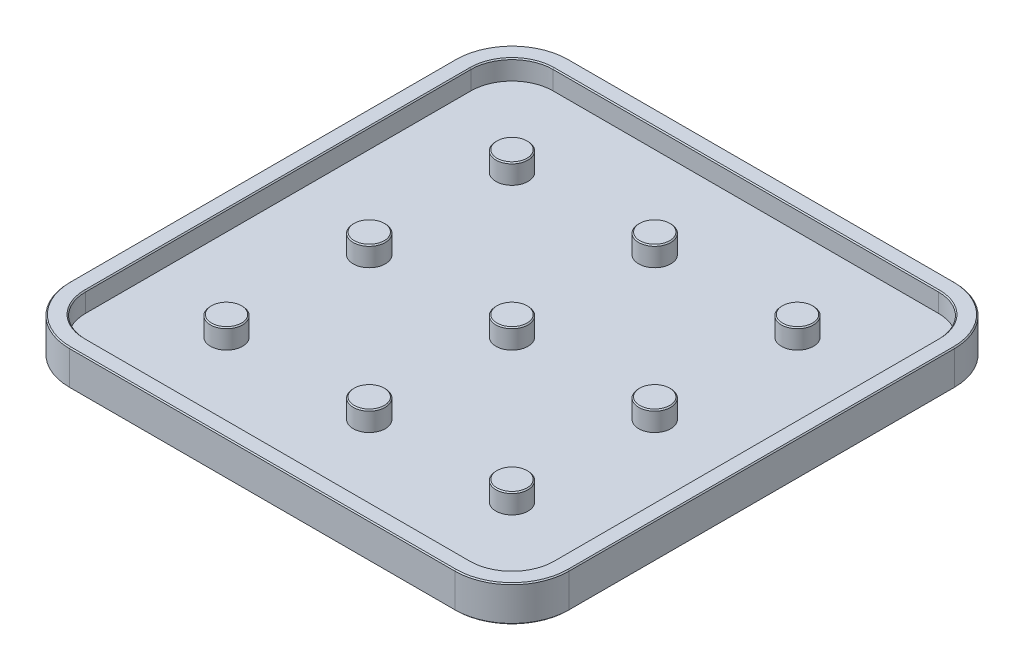
SolidWorks part; units mm, degrees
ref_plane "Front Plane" through (0, 0, 0) normal (0, 0, 1) x (1, 0, 0)
ref_plane "Top Plane" through (0, 0, 0) normal (0, 1, 0) x (1, 0, 0)
ref_plane "Right Plane" through (0, 0, 0) normal (1, 0, 0) x (0, 0, -1)
sketch "Sketch1" plane through (0, 0, 0) normal (0, 1, 0) x (1, 0, 0)
  line L1 (-35, -35) -> (35, -35)
  line L2 (-35, -35) -> (-35, 35)
  line L3 (-35, 35) -> (35, 35)
  line L4 (35, -35) -> (35, 35)
  line L5 (-35, -35) -> (35, 35) construction
  line L6 (-35, 35) -> (35, -35) construction
  point P0 (0, 0)
  dimension "D1" = 70
extrude "Boss-Extrude1" add sketch "Sketch1" against normal mid plane 5
fillet "Fillet1" radius 8 4 edges at (35, 0, -35) (35, 0, 35) (-35, 0, -35) (-35, 0, 35)
sketch "Sketch2" plane through (0, 2.5, 0) normal (0, 1, 0) x (1, 0, 0)
  line L8 (32.75, -27) -> (32.75, 27)
  line L9 (27, 32.75) -> (-27, 32.75)
  line L10 (-32.75, 27) -> (-32.75, -27)
  line L11 (-27, -32.75) -> (27, -32.75)
  line L12 (32.75, -27) -> (32.75, 27)
  line L13 (27, 32.75) -> (-27, 32.75)
  line L14 (-32.75, 27) -> (-32.75, -27)
  line L15 (-27, -32.75) -> (27, -32.75)
  arc A8 (32.75, 27) -> (27, 32.75) centre (27, 27) ccw
  arc A9 (32.75, 27) -> (27, 32.75) centre (27, 27) ccw
  arc A10 (-27, 32.75) -> (-32.75, 27) centre (-27, 27) ccw
  arc A11 (-27, 32.75) -> (-32.75, 27) centre (-27, 27) ccw
  arc A16 (-32.75, -27) -> (-27, -32.75) centre (-27, -27) ccw
  arc A17 (-32.75, -27) -> (-27, -32.75) centre (-27, -27) ccw
  arc A18 (27, -32.75) -> (32.75, -27) centre (27, -27) ccw
  arc A19 (27, -32.75) -> (32.75, -27) centre (27, -27) ccw
  dimension "D1" = 2.25
extrude "Cut-Extrude1" cut sketch "Sketch2" against normal offset from surface (2.75 mm away) 2.25 up to face at (0, -2.5, 0)
sketch "Sketch3" plane through (0, -0.25, 0) normal (0, 1, 0) x (1, 0, 0)
  line L0 (-35, 27) -> (-35, -27) construction
  line L1 (27, 35) -> (-27, 35) construction
  line L2 (-27, -35) -> (27, -35) construction
  line L3 (35, -27) -> (35, 27) construction
  circle A0 centre (-20, 20) radius 2.25
  circle A1 centre (0, 20) radius 2.25
  circle A2 centre (20, 20) radius 2.25
  circle A4 centre (0, 0) radius 2.25
  circle A5 centre (20, 0) radius 2.25
  circle A7 centre (0, -20) radius 2.25
  circle A8 centre (20, -20) radius 2.25
  circle A13 centre (-20, 0) radius 2.25
  circle A14 centre (-20, -20) radius 2.25
  point P40 (-7.6667, 23)
  point P41 (0, 0)
  dimension "D1" = 4.5
  dimension "D2" = 15
  dimension "D3" = 15
  dimension "D6" = 15
  dimension "D7" = 15
  dimension "D4" = 3
  dimension "D5" = 3
extrude "Boss-Extrude2" add sketch "Sketch3" along normal up to surface (2.75 mm away) up to face at (0, 2.5, 0)
chamfer "Chamfer1" distance 0.15 angle 45 33 edges at (-32.6569, -2.5, -32.6569) (-35, -2.5, 0) (-32.6569, -2.5, 32.6569) (0, -2.5, 35) (32.6569, -2.5, 32.6569) (35, -2.5, 0) (32.6569, -2.5, -32.6569) (0, -2.5, -35) (-20, 2.5, 17.75) (-20, 2.5, -2.25) (0, 2.5, -2.25) (0, 2.5, 17.75) (20, 2.5, 17.75) (20, 2.5, -2.25) (0, 2.5, -22.25) (-20, 2.5, -22.25) (20, 2.5, -22.25) (0, 2.5, 32.75) (31.0659, 2.5, 31.0659) (-31.0659, 2.5, 31.0659) (32.75, 2.5, 0) (-32.75, 2.5, 0) (31.0659, 2.5, -31.0659) (-31.0659, 2.5, -31.0659) (0, 2.5, -32.75) (0, 2.5, 35) (32.6569, 2.5, 32.6569) (-32.6569, 2.5, 32.6569) (35, 2.5, 0) (-35, 2.5, 0) (32.6569, 2.5, -32.6569) (-32.6569, 2.5, -32.6569) (0, 2.5, -35)
equation "\"D3@Sketch3\"=\"D2@Sketch3\""
